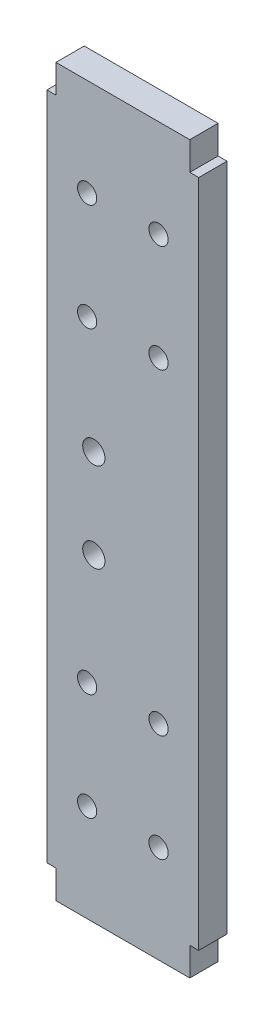
SolidWorks part; units mm, degrees
ref_plane "Front Plane" through (0, 0, 0) normal (0, 0, 1) x (1, 0, 0)
ref_plane "Top Plane" through (0, 0, 0) normal (0, 1, 0) x (1, 0, 0)
ref_plane "Right Plane" through (0, 0, 0) normal (1, 0, 0) x (0, 0, -1)
sketch "Sketch1" plane through (0, 0, 0) normal (0, 0, 1) x (1, 0, 0)
  line L0 (-17, -75) -> (-17, 75)
  line L1 (-17, -75) -> (17, -75)
  line L2 (-17, 75) -> (17, 75)
  line L3 (17, -75) -> (17, 75)
  line L4 (-17, -75) -> (17, 75) construction
  line L5 (-17, 75) -> (17, -75) construction
  point P1 (0, 0)
  dimension "D1" = 34
  dimension "D2" = 150
extrude "Boss-Extrude1" add sketch "Sketch1" along normal blind 6.35
sketch "Sketch3" plane through (0, 0, 6.35) normal (0, 0, 1) x (1, 0, 0)
  line L0 (-15, 81.35) -> (-15, 75)
  line L1 (-15, 81.35) -> (15, 81.35)
  line L2 (-15, 75) -> (15, 75)
  line L3 (15, 81.35) -> (15, 75)
  line L4 (-15, 81.35) -> (15, 75) construction
  line L5 (-15, 75) -> (15, 81.35) construction
  line L6 (-15, -81.35) -> (-15, -75)
  line L7 (-15, -81.35) -> (15, -81.35)
  line L8 (-15, -75) -> (15, -75)
  line L9 (15, -81.35) -> (15, -75)
  line L10 (-15, -81.35) -> (15, -75) construction
  line L11 (-15, -75) -> (15, -81.35) construction
  line L12 (-17, -75) -> (17, -75) construction
  line L13 (17, 75) -> (-17, 75) construction
  point P1 (0, 78.175)
  point P2 (0, -78.175)
  dimension "D1" = 30
  dimension "D2" = 6.35
  dimension "D3" = 6.35
extrude "Boss-Extrude2" add sketch "Sketch3" against normal blind 6.35
sketch "Sketch4" plane through (0, 0, 6.35) normal (0, 0, 1) x (1, 0, 0)
  line L0 (-8, 35.5) -> (-8, 59.5) construction
  line L1 (-8, 35.5) -> (8, 35.5) construction
  line L2 (-8, 59.5) -> (8, 59.5) construction
  line L3 (8, 35.5) -> (8, 59.5) construction
  line L4 (-8, 35.5) -> (8, 59.5) construction
  line L5 (-8, 59.5) -> (8, 35.5) construction
  line L6 (-8, -35.5) -> (-8, -59.5) construction
  line L7 (-8, -35.5) -> (8, -35.5) construction
  line L8 (-8, -59.5) -> (8, -59.5) construction
  line L9 (8, -35.5) -> (8, -59.5) construction
  line L10 (-8, -35.5) -> (8, -59.5) construction
  line L11 (-8, -59.5) -> (8, -35.5) construction
  line L12 (0, -47.5) -> (0, 47.5) construction
  point P1 (0, 47.5)
  point P2 (0, -47.5)
  point P14 (0, 0)
  dimension "D1" = 24
  dimension "D2" = 16
  dimension "D3" = 24
  dimension "D4" = 16
  dimension "D5" = 95
hole_wizard "#8 Clearance Hole1" positions "Sketch6" profile "Sketch5" hole size "#8" standard "ANSI Inch" end condition through all
sketch "Sketch6" plane through (0, 0, 6.35) normal (0, 0, 1) x (1, 0, 0)
  point P0 (-8, 59.5)
  point P3 (8, 59.5)
  point P6 (8, 35.5)
  point P9 (-8, 35.5)
  point P12 (-8, -35.5)
  point P15 (-8, -59.5)
  point P18 (8, -59.5)
  point P21 (8, -35.5)
sketch "Sketch5" plane through (-8, 59.5, 6.35) normal (1, 0, 0) x (0, -1, 0)
  line L0 (0, 0) -> (0, 6.35)
  line L1 (0, 6.35) -> (2.1526, 6.35)
  line L2 (2.1526, 6.35) -> (2.1526, 0)
  line L5 (2.1526, 0) -> (0, 0)
  line L11 (0, -6.35) -> (0, 107.95) construction
  dimension "Thru Hole Dia." = 4.3053
  dimension "Thru Hole Depth" = 6.35
sketch "Sketch7" plane through (0, 0, 6.35) normal (0, 0, 1) x (1, 0, 0)
  line L0 (-6.5, 10) -> (-6.5, -10) construction
  point P2 (-6.5, 0)
  dimension "D1" = 6.5
  dimension "D2" = 20
hole_wizard "#10 Clearance Hole1" positions "Sketch11" profile "Sketch10" hole size "#10" standard "ANSI Inch" end condition through all
sketch "Sketch11" plane through (0, 0, 6.35) normal (0, 0, 1) x (1, 0, 0)
  point P0 (-6.5, 10)
  point P3 (-6.5, -10)
sketch "Sketch10" plane through (-6.5, 10, 6.35) normal (1, 0, 0) x (0, -1, 0)
  line L0 (0, 0) -> (0, 6.35)
  line L1 (0, 6.35) -> (2.4892, 6.35)
  line L2 (2.4892, 6.35) -> (2.4892, 0)
  line L5 (2.4892, 0) -> (0, 0)
  line L11 (0, -6.35) -> (0, 107.95) construction
  dimension "Thru Hole Dia." = 4.9784
  dimension "Thru Hole Depth" = 6.35
